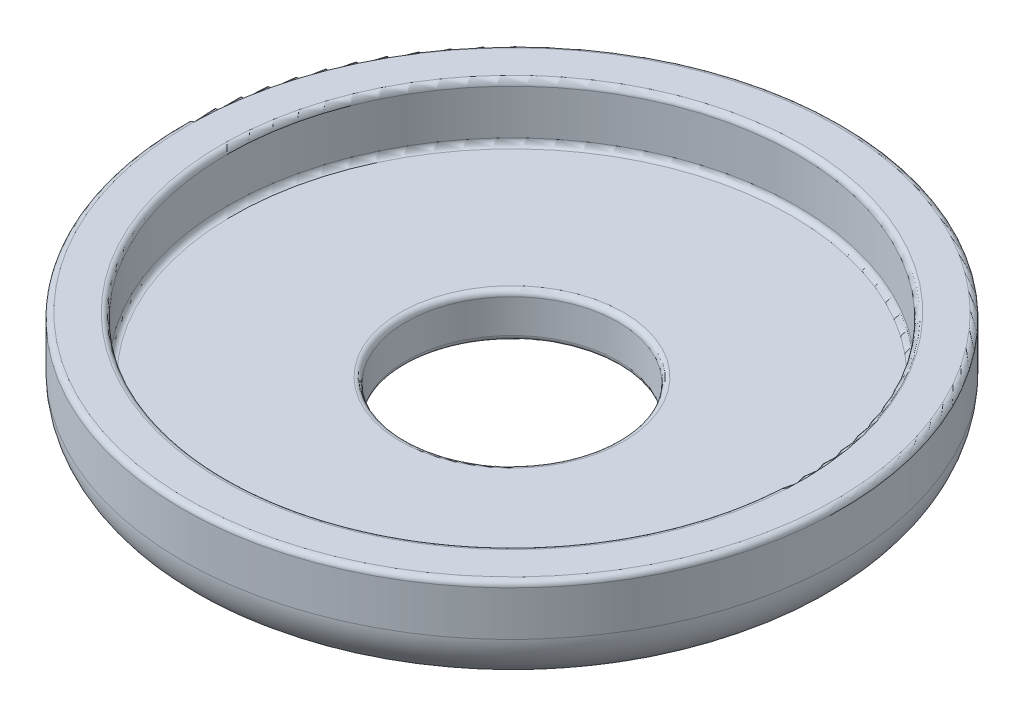
SolidWorks part; units mm, degrees
ref_plane "Front Plane" through (0, 0, 0) normal (0, 0, 1) x (1, 0, 0)
ref_plane "Top Plane" through (0, 0, 0) normal (0, 1, 0) x (1, 0, 0)
ref_plane "Right Plane" through (0, 0, 0) normal (1, 0, 0) x (0, 0, -1)
sketch "Sketch1" plane through (0, 0, 0) normal (0, 0, 1) x (1, 0, 0)
  line L0 (0, 0) -> (0, 11.8971) construction
  line L1 (5, 0) -> (12.5, 0)
  line L5 (12.5, 2) -> (5, 2)
  line L6 (4.75, 1.75) -> (4.75, 0.25)
  line L7 (12.75, 2.25) -> (12.75, 4.25)
  line L8 (13, 4.5) -> (14.5, 4.5)
  line L9 (14.75, 4.25) -> (14.75, 2.25)
  arc A0 (12.5, 0) -> (14.75, 2.25) centre (12.5, 2.25) ccw
  arc A1 (5, 2) -> (4.75, 1.75) centre (5, 1.75) ccw
  arc A2 (14.5, 4.5) -> (14.75, 4.25) centre (14.5, 4.25) cw
  arc A3 (12.75, 4.25) -> (13, 4.5) centre (13, 4.25) cw
  arc A4 (12.75, 2.25) -> (12.5, 2) centre (12.5, 2.25) cw
  arc A5 (5, 0) -> (4.75, 0.25) centre (5, 0.25) cw
  dimension "D6" = 2.25
  dimension "D7" = 0.25
  dimension "D1" = 4.75
  dimension "D2" = 2
  dimension "D3" = 2
  dimension "D4" = 4.5
  dimension "D5" = 14.75
revolve "Revolve1" add sketch "Sketch1" angle 360 about L0
